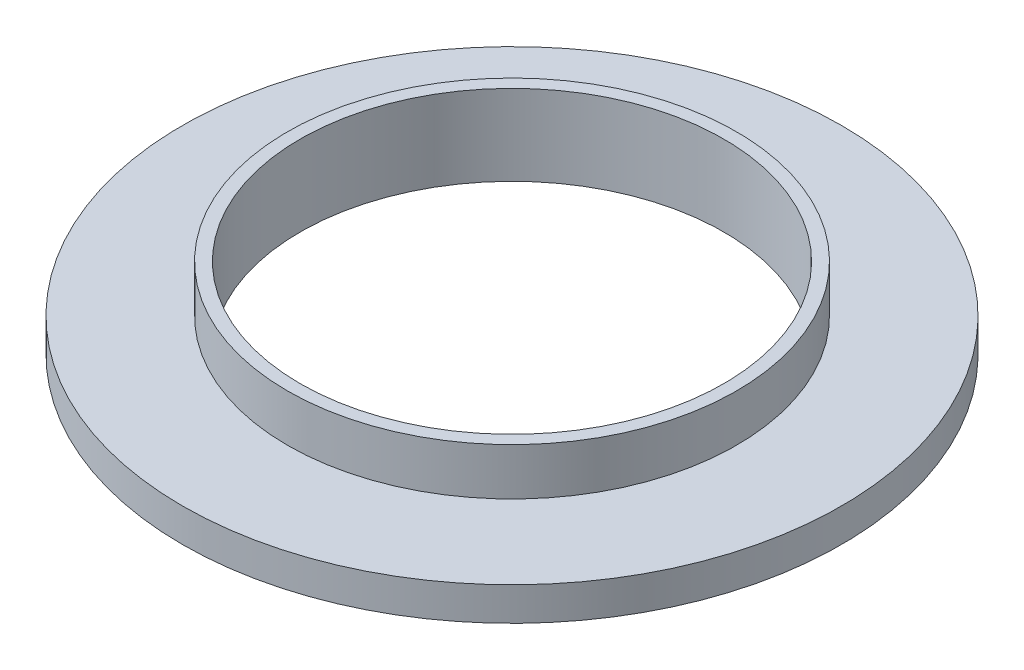
SolidWorks part; units mm, degrees
ref_plane "Front Plane" through (0, 0, 0) normal (0, 0, 1) x (1, 0, 0)
ref_plane "Top Plane" through (0, 0, 0) normal (0, 1, 0) x (1, 0, 0)
ref_plane "Right Plane" through (0, 0, 0) normal (1, 0, 0) x (0, 0, -1)
sketch "Sketch1" plane through (0, 0, 0) normal (0, 1, 0) x (1, 0, 0)
  circle A0 centre (0, 0) radius 14
  circle A1 centre (0, 0) radius 9
  dimension "D1" = 18
  dimension "D2" = 28
extrude "Boss-Extrude1" add sketch "Sketch1" along normal blind 1.42
sketch "Sketch2" plane through (0, 1.42, 0) normal (0, 1, 0) x (1, 0, 0)
  circle A0 centre (0, 0) radius 9 construction
  circle A1 centre (0, 0) radius 9
  circle A2 centre (0, 0) radius 9.5377
  dimension "D1" = 19.0754
extrude "Boss-Extrude2" add sketch "Sketch2" along normal blind 2
